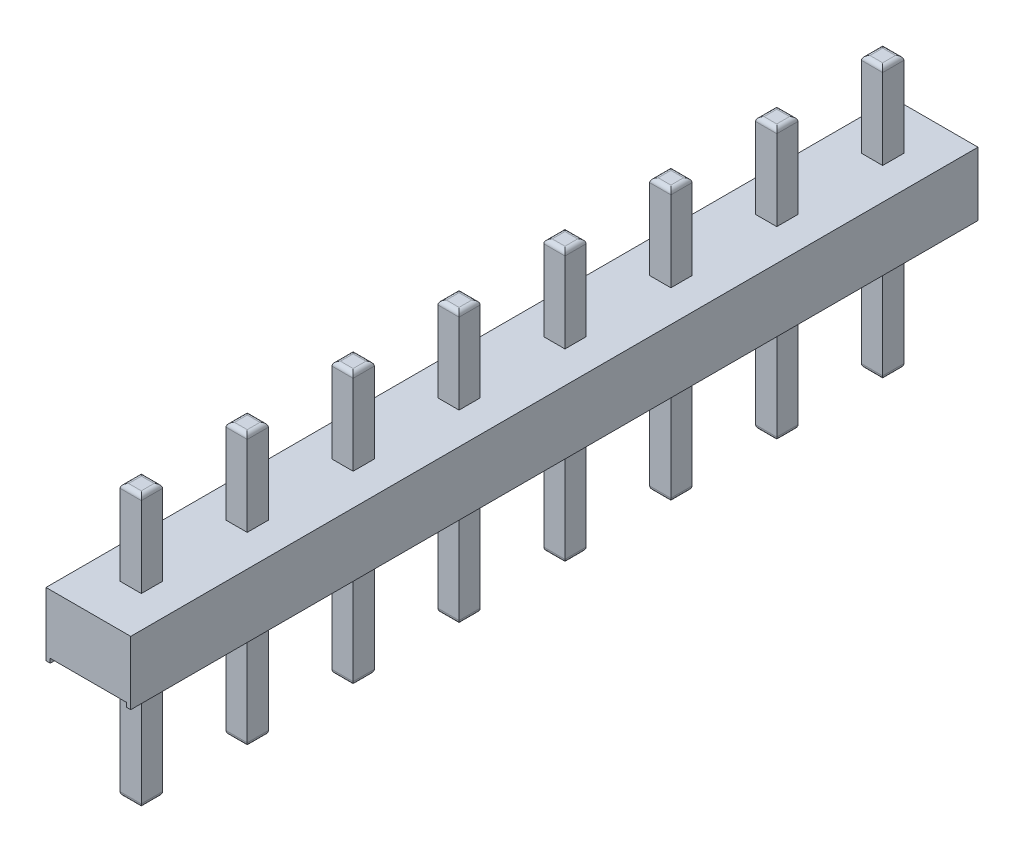
SolidWorks part; units mm, degrees
material "黄銅"
ref_plane "Front Plane" through (0, 0, 0) normal (0, 0, 1) x (1, 0, 0)
ref_plane "Top Plane" through (0, 0, 0) normal (0, 1, 0) x (1, 0, 0)
ref_plane "Right Plane" through (0, 0, 0) normal (1, 0, 0) x (0, 0, -1)
sketch "Sketch1" plane through (0, 0, 0) normal (0, 0, 1) x (1, 0, 0)
  line L0 (0.1, -1.5) -> (0.1, -1.3997)
  line L1 (0, 0) -> (2, 0)
  line L2 (0, 0) -> (0, -1.5)
  line L3 (0, -1.5) -> (0.1, -1.5)
  line L4 (2, 0) -> (2, -1.5)
  line L5 (0.1, -1.3997) -> (1.9019, -1.3997)
  line L6 (1.9019, -1.3997) -> (1.9019, -1.5)
  line L7 (1.9019, -1.5) -> (2, -1.5)
  dimension "D1" = 2
  dimension "D2" = 1.5
  dimension "D3" = 0.1
extrude "Boss-Extrude1" add sketch "Sketch1" against normal blind 20
sketch "Sketch2" plane through (0, 0, 0) normal (0, 1, 0) x (1, 0, 0)
  line L0 (2, 0) -> (0, 0) construction
  line L1 (0.75, 4) -> (1.25, 4)
  line L2 (0.75, 4) -> (0.75, 3.5)
  line L3 (0.75, 1.5) -> (1.25, 1.5)
  line L4 (0.75, 1.5) -> (0.75, 1)
  line L5 (0.75, 1) -> (1.25, 1)
  line L6 (1.25, 1.5) -> (1.25, 1)
  line L7 (0.75, 1.5) -> (1.25, 1) construction
  line L8 (0.75, 1) -> (1.25, 1.5) construction
  line L9 (2, 20) -> (2, 0) construction
  line L10 (1.25, 4) -> (1.25, 3.5)
  line L11 (0.75, 3.5) -> (1.25, 3.5)
  line L12 (0.75, 6.5) -> (1.25, 6.5)
  line L13 (0.75, 6.5) -> (0.75, 6)
  line L14 (1.25, 6.5) -> (1.25, 6)
  line L15 (0.75, 6) -> (1.25, 6)
  line L16 (0.75, 9) -> (1.25, 9)
  line L17 (0.75, 9) -> (0.75, 8.5)
  line L18 (1.25, 9) -> (1.25, 8.5)
  line L19 (0.75, 8.5) -> (1.25, 8.5)
  line L20 (0.75, 11.5) -> (1.25, 11.5)
  line L21 (0.75, 11.5) -> (0.75, 11)
  line L22 (1.25, 11.5) -> (1.25, 11)
  line L23 (0.75, 11) -> (1.25, 11)
  line L24 (0.75, 14) -> (1.25, 14)
  line L25 (0.75, 14) -> (0.75, 13.5)
  line L26 (1.25, 14) -> (1.25, 13.5)
  line L27 (0.75, 13.5) -> (1.25, 13.5)
  line L28 (0.75, 16.5) -> (1.25, 16.5)
  line L29 (0.75, 16.5) -> (0.75, 16)
  line L30 (1.25, 16.5) -> (1.25, 16)
  line L31 (0.75, 16) -> (1.25, 16)
  line L32 (0.75, 19) -> (1.25, 19)
  line L33 (0.75, 19) -> (0.75, 18.5)
  line L34 (1.25, 19) -> (1.25, 18.5)
  line L35 (0.75, 18.5) -> (1.25, 18.5)
  point P0 (1, 1.25)
  dimension "D1" = 0.5
  dimension "D2" = 0.5
  dimension "D3" = 1
  dimension "D4" = 1
  dimension "D5" = 8
extrude "Boss-Extrude2" add sketch "Sketch2" along normal blind 2
sketch "Sketch3" plane through (0, -1.3997, 0) normal (0, -1, 0) x (-1, 0, 0)
  line L0 (0, 20) -> (0, 0) construction
  line L1 (-1.25, 1.5) -> (-0.75, 1.5)
  line L2 (-1.25, 1.5) -> (-1.25, 1)
  line L3 (-1.25, 1) -> (-0.75, 1)
  line L4 (-0.75, 1.5) -> (-0.75, 1)
  line L6 (-1.25, 1.5) -> (-0.75, 1) construction
  line L8 (-1.25, 1) -> (-0.75, 1.5) construction
  line L10 (-0.1, 0) -> (-1.9019, 0) construction
  line L11 (-1.25, 4) -> (-0.75, 4)
  line L12 (-1.25, 4) -> (-1.25, 3.5)
  line L13 (-0.75, 4) -> (-0.75, 3.5)
  line L14 (-1.25, 3.5) -> (-0.75, 3.5)
  line L15 (-1.25, 6.5) -> (-0.75, 6.5)
  line L16 (-1.25, 6.5) -> (-1.25, 6)
  line L17 (-0.75, 6.5) -> (-0.75, 6)
  line L18 (-1.25, 6) -> (-0.75, 6)
  line L19 (-1.25, 9) -> (-0.75, 9)
  line L20 (-1.25, 9) -> (-1.25, 8.5)
  line L21 (-0.75, 9) -> (-0.75, 8.5)
  line L22 (-1.25, 8.5) -> (-0.75, 8.5)
  line L23 (-1.25, 11.5) -> (-0.75, 11.5)
  line L24 (-1.25, 11.5) -> (-1.25, 11)
  line L25 (-0.75, 11.5) -> (-0.75, 11)
  line L26 (-1.25, 11) -> (-0.75, 11)
  line L27 (-1.25, 14) -> (-0.75, 14)
  line L28 (-1.25, 14) -> (-1.25, 13.5)
  line L29 (-0.75, 14) -> (-0.75, 13.5)
  line L30 (-1.25, 13.5) -> (-0.75, 13.5)
  line L31 (-1.25, 16.5) -> (-0.75, 16.5)
  line L32 (-1.25, 16.5) -> (-1.25, 16)
  line L33 (-0.75, 16.5) -> (-0.75, 16)
  line L34 (-1.25, 16) -> (-0.75, 16)
  line L35 (-1.25, 19) -> (-0.75, 19)
  line L36 (-1.25, 19) -> (-1.25, 18.5)
  line L37 (-0.75, 19) -> (-0.75, 18.5)
  line L38 (-1.25, 18.5) -> (-0.75, 18.5)
  point P0 (-1, 1.25)
  dimension "D1" = 0.5
  dimension "D2" = 0.5
  dimension "D3" = 1
  dimension "D4" = 1.25
extrude "Boss-Extrude3" add sketch "Sketch3" along normal blind 3
fillet "Fillet2" radius 0.1 64 edges at (1, 2, -1) (0.75, 2, -1.25) (1, 2, -1.5) (1.25, 2, -1.25) (1, 2, -3.5) (0.75, 2, -3.75) (1, 2, -4) (1.25, 2, -3.75) (1, 2, -6) (0.75, 2, -6.25) (1, 2, -6.5) (1.25, 2, -6.25) (1, 2, -8.5) (0.75, 2, -8.75) (1, 2, -9) (1.25, 2, -8.75) (1, 2, -11) (0.75, 2, -11.25) (1, 2, -11.5) (1.25, 2, -11.25) (1, 2, -13.5) (1.25, 2, -13.75) (0.75, 2, -13.75) (1, 2, -14) (1, 2, -16) (0.75, 2, -16.25) (1, 2, -16.5) (1.25, 2, -16.25) (1, 2, -18.5) (1.25, 2, -18.75) (0.75, 2, -18.75) (1, 2, -19) (1, -4.3997, -1) (1.25, -4.3997, -1.25) (1, -4.3997, -1.5) (0.75, -4.3997, -1.25) (1.25, -4.3997, -3.75) (1, -4.3997, -3.5) (1, -4.3997, -4) (0.75, -4.3997, -3.75) (1, -4.3997, -6) (1.25, -4.3997, -6.25) (1, -4.3997, -6.5) (0.75, -4.3997, -6.25) (1.25, -4.3997, -8.75) (1, -4.3997, -8.5) (0.75, -4.3997, -8.75) (1, -4.3997, -9) (1, -4.3997, -11) (1.25, -4.3997, -11.25) (1, -4.3997, -11.5) (0.75, -4.3997, -11.25) (1, -4.3997, -13.5) (1.25, -4.3997, -13.75) (1, -4.3997, -14) (0.75, -4.3997, -13.75) (1.25, -4.3997, -16.25) (1, -4.3997, -16) (1, -4.3997, -16.5) (0.75, -4.3997, -16.25) (1, -4.3997, -19) (1.25, -4.3997, -18.75) (1, -4.3997, -18.5) (0.75, -4.3997, -18.75)
